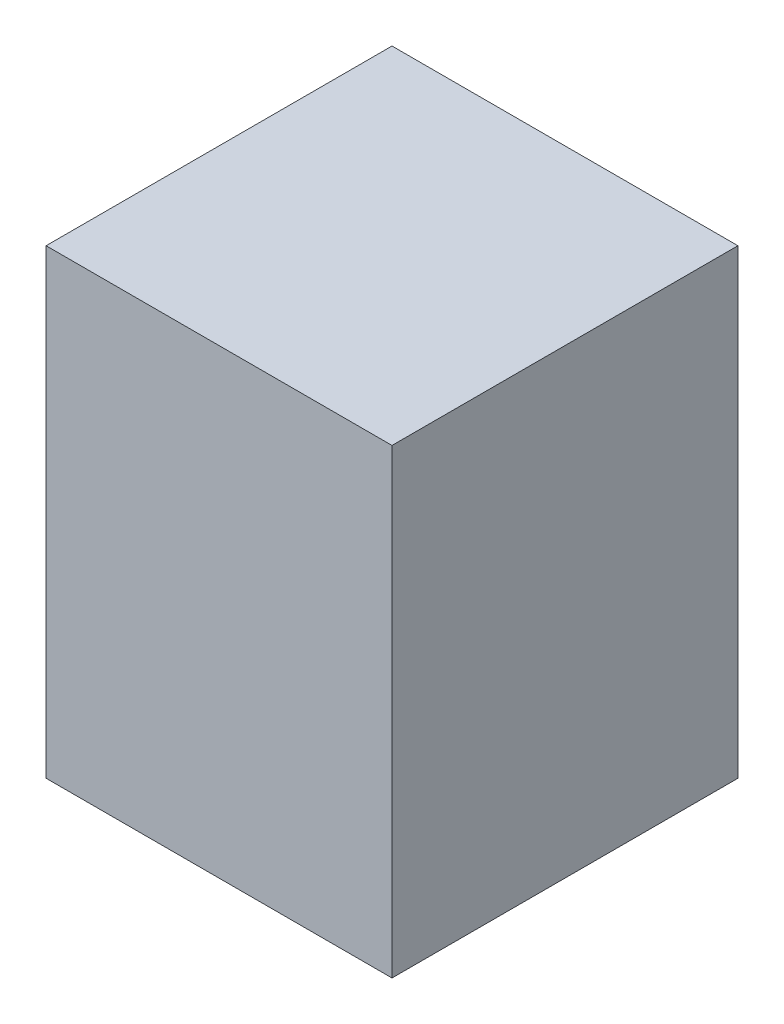
SolidWorks part; units mm, degrees
ref_plane "Front Plane" through (0, 0, 0) normal (0, 0, 1) x (1, 0, 0)
ref_plane "Top Plane" through (0, 0, 0) normal (0, 1, 0) x (1, 0, 0)
ref_plane "Right Plane" through (0, 0, 0) normal (1, 0, 0) x (0, 0, -1)
sketch "Sketch1" plane through (0, 0, 0) normal (0, 1, 0) x (1, 0, 0)
  line L1 (0, 0) -> (19.05, 0)
  line L2 (0, 0) -> (0, 19.05)
  line L3 (0, 19.05) -> (19.05, 19.05)
  line L4 (19.05, 0) -> (19.05, 19.05)
  dimension "D1" = 19.05
extrude "Boss-Extrude1" add sketch "Sketch1" along normal blind 25.4
